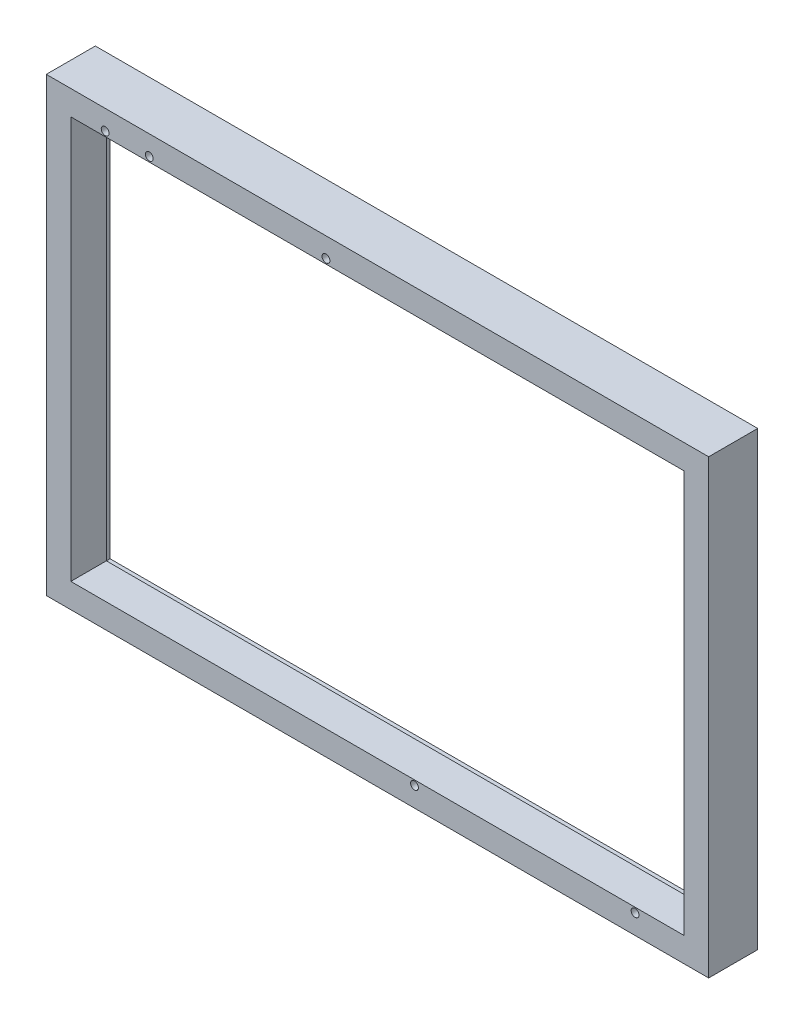
SolidWorks part; units mm, degrees
ref_plane "Спереди" through (0, 0, 0) normal (0, 0, 1) x (1, 0, 0)
ref_plane "Сверху" through (0, 0, 0) normal (0, 1, 0) x (1, 0, 0)
ref_plane "Справа" through (0, 0, 0) normal (1, 0, 0) x (0, 0, -1)
sketch "Эскиз1" plane through (0, 0, 0) normal (0, 0, 1) x (1, 0, 0)
  line L1 (0, 0) -> (125, 0)
  line L2 (0, 0) -> (0, 82)
  line L3 (0, 82) -> (125, 82)
  line L4 (125, 0) -> (125, 82)
  line L5 (-5, -5) -> (130, -5)
  line L6 (-5, -5) -> (-5, 87)
  line L7 (-5, 87) -> (130, 87)
  line L8 (130, -5) -> (130, 87)
  circle A2 centre (7, 83) radius 0.8
  circle A3 centre (115, -1) radius 0.8
  circle A4 centre (16, 83) radius 0.8
  circle A5 centre (52, 83) radius 0.8
  circle A6 centre (70.05, -1) radius 0.8
  point P19 (0, 0)
extrude "Бобышка-Вытянуть1" add sketch "Эскиз1" along normal blind 10 and the other way blind 0.0001
sketch "Эскиз4" plane through (0, 0, -0.0001) normal (0, 0, -1) x (-1, 0, 0)
  line L1 (-127, -2) -> (2, -2)
  line L2 (-127, -2) -> (-127, 84)
  line L3 (-127, 84) -> (2, 84)
  line L4 (2, -2) -> (2, 84)
  point P4 (0, 0)
  point P5 (2.2491, 84.0019)
extrude "Вырез-Вытянуть1" cut sketch "Эскиз4" against normal blind 2.75
